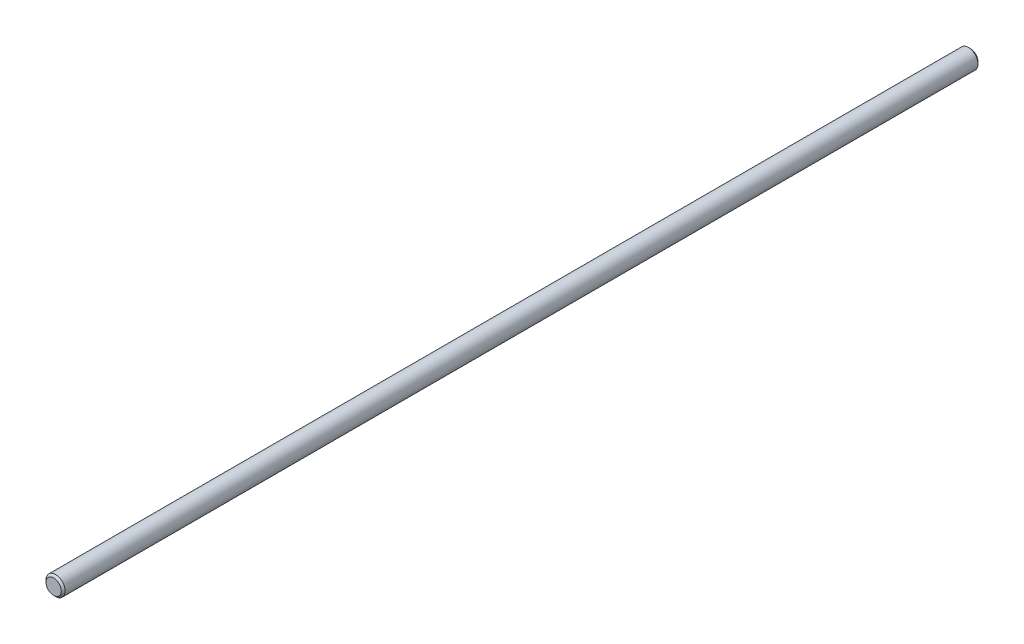
SolidWorks part; units mm, degrees
ref_plane "Front" through (0, 0, 0) normal (0, 0, 1) x (1, 0, 0)
ref_plane "Top" through (0, 0, 0) normal (0, 1, 0) x (1, 0, 0)
ref_plane "Right" through (0, 0, 0) normal (1, 0, 0) x (0, 0, -1)
sketch "Sketch1" plane through (0, 0, 0) normal (0, 0, 1) x (1, 0, 0)
  circle A0 centre (0, 0) radius 3.175
  dimension "dia" = 6.35
extrude "Extrude1" add sketch "Sketch1" along normal mid plane 304.8
sketch "Sketch2" plane through (0, 0, 0) normal (1, 0, 0) x (0, 0, -1)
  point P0 (-152.4, 3.175)
  point P1 (152.4, 3.175)
chamfer "Chamfer1" distance 0.635 angle 45 2 edges at (3.175, 0, -152.4) (3.175, 0, 152.4)
equation "\"D1@Chamfer1\" = \"dia@Sketch1\" * .1"
